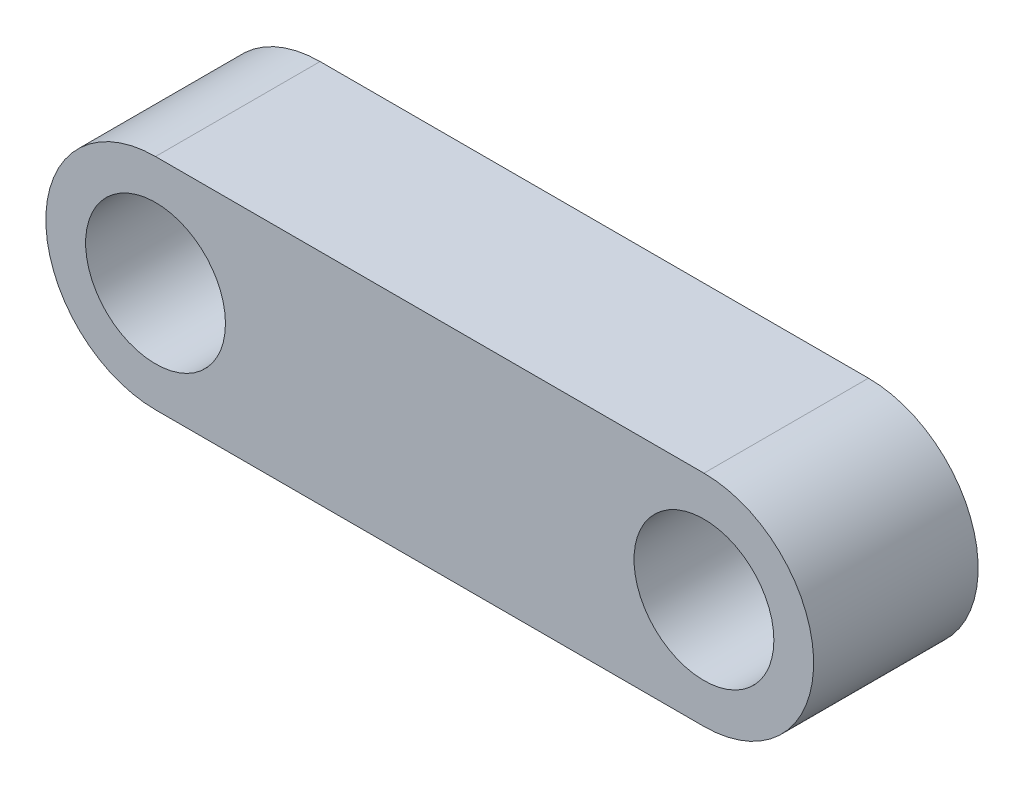
SolidWorks part; units mm, degrees
material "Клен"
ref_plane "Спереди" through (0, 0, 0) normal (0, 0, 1) x (1, 0, 0)
ref_plane "Сверху" through (0, 0, 0) normal (0, 1, 0) x (1, 0, 0)
ref_plane "Справа" through (0, 0, 0) normal (1, 0, 0) x (0, 0, -1)
sketch "Эскиз1" plane through (0, 0, 0) normal (0, 0, 1) x (1, 0, 0)
  line L0 (0, -6.7272) -> (-0.2429, 7.8829) construction
  line L1 (10, -4) -> (5, -4)
  line L2 (5, -4) -> (-10, -4)
  line L3 (10, 4) -> (-10, 4)
  arc A0 (10, -4) -> (10, 4) centre (10, 0) ccw
  arc A1 (-10, -4) -> (-10, 4) centre (-10, 0) cw
  circle A2 centre (10, 0) radius 2.55
  circle A3 centre (-10, 0) radius 2.55
extrude "Бобышка-Вытянуть1" add sketch "Эскиз1" along normal blind 6
